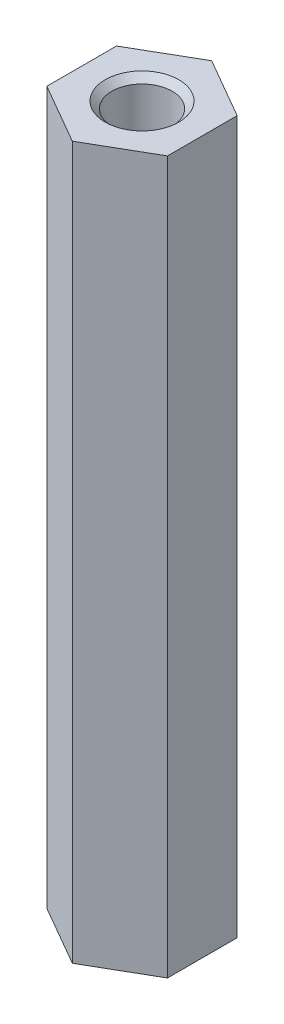
SolidWorks part; units mm, degrees
material "6061 Alloy"
ref_plane "Front Plane" through (0, 0, 0) normal (0, 0, 1) x (1, 0, 0)
ref_plane "Top Plane" through (0, 0, 0) normal (0, 1, 0) x (1, 0, 0)
ref_plane "Right Plane" through (0, 0, 0) normal (1, 0, 0) x (0, 0, -1)
sketch "Sketch1" plane through (0, 0, 0) normal (0, 1, 0) x (1, 0, 0)
  line L1 (-2.5, 1.4434) -> (-2.5, -1.4434)
  line L2 (-2.5, -1.4434) -> (0, -2.8868)
  line L3 (0, -2.8868) -> (2.5, -1.4434)
  line L4 (2.5, -1.4434) -> (2.5, 1.4434)
  line L5 (2.5, 1.4434) -> (0, 2.8868)
  line L6 (0, 2.8868) -> (-2.5, 1.4434)
  circle A0 centre (0, 0) radius 2.5 construction
  dimension "D1" = 5
extrude "Boss-Extrude1" add sketch "Sketch1" along normal blind 29.5
hole_wizard "M3 Tapped Hole1" positions "Sketch2" profile "Sketch3" tap size "M3" standard "ISO"
sketch "Sketch2" plane through (0, 29.5, 0) normal (0, 1, 0) x (1, 0, 0)
  point P0 (0, 0)
sketch "Sketch3" plane through (0, 29.5, 0) normal (1, 0, 0) x (0, 0, 1)
  line L0 (0, 0) -> (0, 8.2511)
  line L1 (0, 8.2511) -> (1.25, 7.5)
  line L2 (1.25, 7.5) -> (1.25, 0.275)
  line L3 (1.25, 0.275) -> (1.525, 0)
  line L5 (1.525, 0) -> (0, 0)
  line L6 (-1.25, 0.275) -> (-1.525, 0) construction
  line L10 (0, 8.2511) -> (-1.25, 7.5) construction
  line L11 (0, -6.35) -> (0, 107.95) construction
  dimension "Tap Drill Dia." = 2.5
  dimension "Tap Drill Depth" = 7.5
  dimension "Near C'Sink Dia." = 3.05
  dimension "Near C'Sink Angle" = 90
  dimension "Drill Angle" = 118
cosmetic thread "Hole Thread1" parameters "D1"=6, "D2"=3
hole_wizard "M3 Tapped Hole2" positions "Sketch4" profile "Sketch5" tap size "M3" standard "ISO"
sketch "Sketch4" plane through (0, 0, 0) normal (0, -1, 0) x (-1, 0, 0)
  point P0 (0, 0)
sketch "Sketch5" plane through (0, 0, 0) normal (1, 0, 0) x (0, 0, -1)
  line L0 (0, 0) -> (0, 8.2511)
  line L1 (0, 8.2511) -> (1.25, 7.5)
  line L2 (1.25, 7.5) -> (1.25, 0.275)
  line L3 (1.25, 0.275) -> (1.525, 0)
  line L5 (1.525, 0) -> (0, 0)
  line L6 (-1.25, 0.275) -> (-1.525, 0) construction
  line L10 (0, 8.2511) -> (-1.25, 7.5) construction
  line L11 (0, -6.35) -> (0, 107.95) construction
  dimension "Tap Drill Dia." = 2.5
  dimension "Tap Drill Depth" = 7.5
  dimension "Near C'Sink Dia." = 3.05
  dimension "Near C'Sink Angle" = 90
  dimension "Drill Angle" = 118
cosmetic thread "Hole Thread2" parameters "D1"=6, "D2"=3
